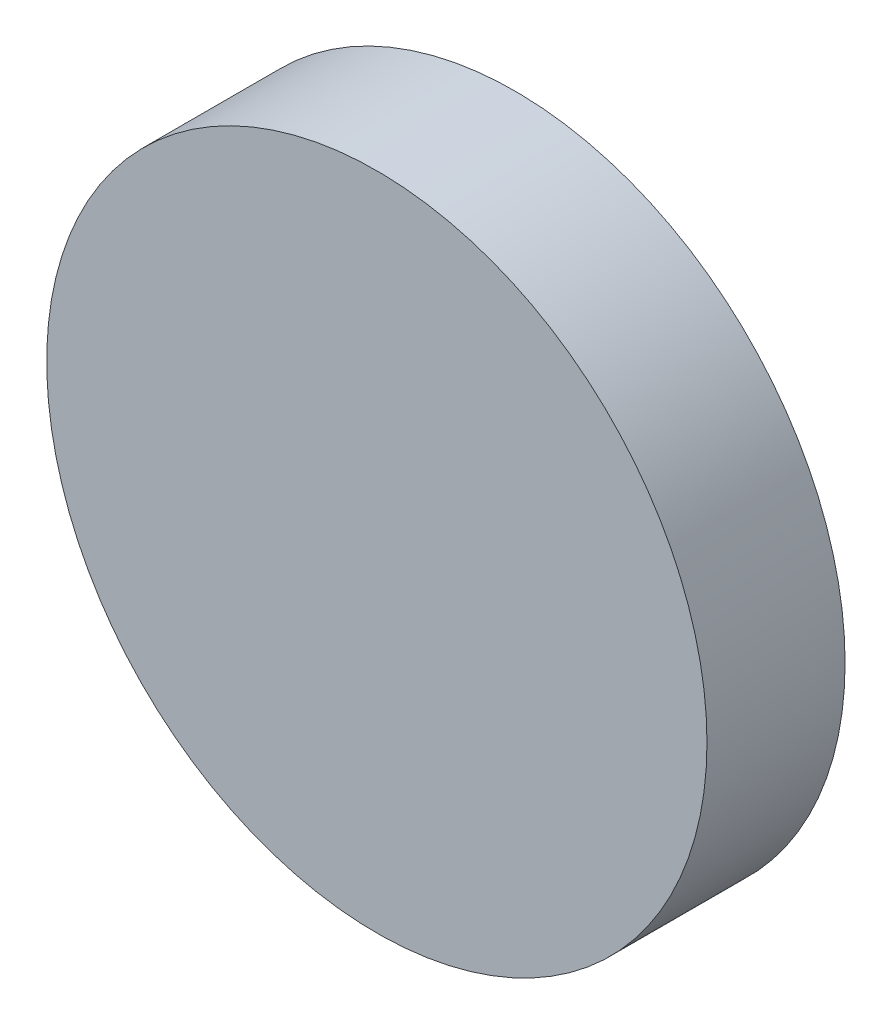
SolidWorks part; units mm, degrees
material "6061-T6 (SS)"
ref_plane "Front Plane" through (0, 0, 0) normal (0, 0, 1) x (1, 0, 0)
ref_plane "Top Plane" through (0, 0, 0) normal (0, 1, 0) x (1, 0, 0)
ref_plane "Right Plane" through (0, 0, 0) normal (1, 0, 0) x (0, 0, -1)
sketch "Sketch1" plane through (0, 0, 0) normal (0, 0, 1) x (1, 0, 0)
  circle A0 centre (0, 0) radius 45.5359
  dimension "D1" = 91.0717
extrude "Boss-Extrude1" add sketch "Sketch1" along normal blind 19.05
